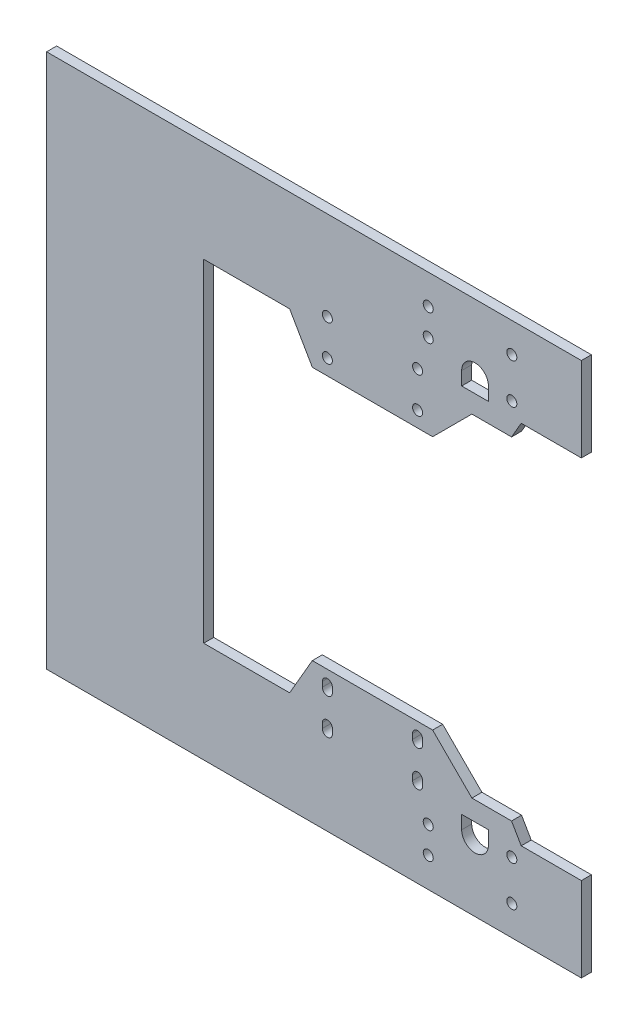
SolidWorks part; units mm, degrees
ref_plane "Front Plane" through (0, 0, 0) normal (0, 0, 1) x (1, 0, 0)
ref_plane "Top Plane" through (0, 0, 0) normal (0, 1, 0) x (1, 0, 0)
ref_plane "Right Plane" through (0, 0, 0) normal (1, 0, 0) x (0, 0, -1)
sketch "Sketch2" plane through (0, 0, 0) normal (0, 0, 1) x (1, 0, 0)
  line L0 (-102, 23.75) -> (-102, 0) construction
  line L1 (3, 49.75) -> (-110, 49.75)
  line L2 (3, 49.75) -> (3, -49.75)
  line L3 (3, -49.75) -> (-110, -49.75)
  line L4 (-110, 49.75) -> (-110, -49.75)
  line L5 (-97.0774, 39.75) -> (-88.9226, 39.75) construction
  line L6 (-77, 0) -> (-110, 0) construction
  line L7 (-77, -33) -> (-77, 33) construction
  line L10 (3, -30) -> (3, 30) construction
  line L11 (-110, 0) -> (-157, 0) construction
  line L12 (3, 80) -> (-157, 80)
  line L13 (3, 80) -> (3, -80)
  line L14 (3, -80) -> (-157, -80)
  line L15 (-157, 80) -> (-157, -80)
  dimension "D1" = 8
  dimension "D2" = 10
  dimension "D3" = 160
  dimension "D4" = 160
extrude "Boss-Extrude1" add sketch "Sketch2" along normal blind 3 contours L12 L15 L14 L13 L3 L4 L1
sketch "Sketch3" plane through (0, 0, 3) normal (0, 0, 1) x (1, 0, 0)
  line L0 (-77.5, 38) -> (-41.5, 38)
  line L1 (-41.5, 38) -> (-29.75, 49.75)
  line L2 (3, 49.75) -> (-110, 49.75) construction
  line L3 (-29.75, 49.75) -> (-84.2839, 49.75)
  line L4 (-84.2839, 49.75) -> (-77.5, 38)
  line L5 (-77.5, 38) -> (-77.5, 55) construction
  line L6 (-110, 0) -> (98.0736, 0) construction
  line L7 (-110, 49.75) -> (-110, -49.75) construction
  line L8 (-29.75, -49.75) -> (-84.2839, -49.75)
  line L9 (-41.5, -38) -> (-29.75, -49.75)
  line L10 (-77.5, -38) -> (-41.5, -38)
  line L11 (-84.2839, -49.75) -> (-77.5, -38)
  dimension "D1" = 45
  dimension "D2" = 30
extrude "Boss-Extrude2" add sketch "Sketch3" against normal up to surface (3 mm away) up to face at (-65.25, 0, 0)
sketch "Sketch4" plane through (0, 0, 3) normal (0, 0, 1) x (1, 0, 0)
  line L0 (-17.8868, -49.75) -> (-15, -54.75)
  line L1 (3, -49.75) -> (-29.75, -49.75) construction
  line L2 (-15, -54.75) -> (3, -54.75)
  line L3 (3, -49.75) -> (3, -80) construction
  line L4 (3, -54.75) -> (3, -49.75)
  line L5 (3, -49.75) -> (-17.8868, -49.75)
  line L6 (-110, 0) -> (99.4713, 0) construction
  line L7 (-110, 49.75) -> (-110, -49.75) construction
  line L8 (-17.8868, 49.75) -> (-15, 54.75)
  line L9 (3, 49.75) -> (-17.8868, 49.75)
  line L10 (3, 54.75) -> (3, 49.75)
  line L11 (-15, 54.75) -> (3, 54.75)
  dimension "D1" = 18
  dimension "D2" = 5
  dimension "D3" = 60
extrude "Cut-Extrude1" cut sketch "Sketch4" against normal through all
sketch "Sketch5" plane through (0, 0, 3) normal (0, 0, 1) x (1, 0, 0)
  circle A0 centre (-73, -42.65) radius 1.5 construction
  circle A1 centre (-46, -42.65) radius 1.5 construction
  circle A2 centre (-73, -42.65) radius 1.5
  circle A3 centre (-46, -42.65) radius 1.5
  circle A4 centre (-46, -53.35) radius 1.5 construction
  circle A5 centre (-73, -53.35) radius 1.5 construction
  circle A6 centre (-46, -53.35) radius 1.5
  circle A7 centre (-73, -53.35) radius 1.5
  circle A8 centre (-46, 42.65) radius 1.5 construction
  circle A9 centre (-73, 42.65) radius 1.5 construction
  circle A10 centre (-46, 42.65) radius 1.5
  circle A11 centre (-73, 42.65) radius 1.5
  circle A12 centre (-73, 53.35) radius 1.5 construction
  circle A13 centre (-73, 53.35) radius 1.5
  circle A14 centre (-46, 53.35) radius 1.5 construction
  circle A15 centre (-46, 53.35) radius 1.5
extrude "Cut-Extrude2" cut sketch "Sketch5" against normal blind 10
sketch "Sketch7" plane through (0, 0, 0) normal (0, 0, -1) x (-1, 0, 0)
  circle A0 centre (28.8114, -59.5) radius 4 construction
  circle A1 centre (28.8114, -59.5) radius 4
  circle A2 centre (28.8114, 59.5) radius 4 construction
  circle A3 centre (28.8114, 59.5) radius 4
extrude "Cut-Extrude3" cut sketch "Sketch7" against normal blind 6
sketch "Sketch8" plane through (0, 0, 3) normal (0, 0, 1) x (1, 0, 0)
  circle A0 centre (-17.8114, 59.1) radius 1.5 construction
  circle A1 centre (-17.8114, 71.1) radius 1.5 construction
  circle A2 centre (-42.8114, 63.1) radius 1.5 construction
  circle A3 centre (-42.8114, 71.1) radius 1.5 construction
  circle A4 centre (-42.8114, -71.1) radius 1.5 construction
  circle A5 centre (-42.8114, -63.1) radius 1.5 construction
  circle A6 centre (-17.8114, -59.1) radius 1.5 construction
  circle A7 centre (-17.8114, -71.1) radius 1.5 construction
  circle A8 centre (-17.8114, 59.1) radius 1.5
  circle A9 centre (-17.8114, 71.1) radius 1.5
  circle A10 centre (-42.8114, 63.1) radius 1.5
  circle A11 centre (-42.8114, 71.1) radius 1.5
  circle A12 centre (-42.8114, -71.1) radius 1.5
  circle A13 centre (-42.8114, -63.1) radius 1.5
  circle A14 centre (-17.8114, -59.1) radius 1.5
  circle A15 centre (-17.8114, -71.1) radius 1.5
extrude "Cut-Extrude4" cut sketch "Sketch8" against normal blind 4
sketch "Sketch9" plane through (0, 0, 0) normal (0, 0, -1) x (-1, 0, 0)
  line L0 (24.8114, 59.5) -> (24.8114, 55.5)
  line L1 (24.8114, 55.5) -> (32.8114, 55.5)
  line L2 (32.8114, 55.5) -> (32.8114, 59.5)
  line L3 (24.8114, -59.5) -> (24.8114, -55.5)
  line L4 (24.8114, -55.5) -> (28.8114, -55.5)
  line L5 (28.8114, -55.5) -> (32.8114, -55.5)
  line L6 (32.8114, -55.5) -> (32.8114, -59.5)
  line L7 (28.8114, -59.5) -> (28.8114, -55.5) construction
  circle A0 centre (28.8114, 59.5) radius 4 construction
  circle A1 centre (28.8114, 59.5) radius 4
  circle A2 centre (28.8114, -59.5) radius 4 construction
  circle A3 centre (28.8114, -59.5) radius 4
  circle M17 centre (28.8114, -59.5) radius 4
  circle M18 centre (28.8114, 59.5) radius 4
extrude "Cut-Extrude5" cut sketch "Sketch9" against normal blind 10 contours L6 L5 M17 | L4 L3 M17 | L0 L1 M18 | L1 L2 M18
sketch "Sketch10" plane through (0, 0, 0) normal (0, 0, -1) x (-1, 0, 0)
  line L0 (73, -54.1) -> (73, -52.6) construction
  line L1 (71.5, -54.1) -> (71.5, -52.6)
  line L2 (74.5, -54.1) -> (74.5, -52.6)
  line L3 (73, -41.9) -> (73, -43.4) construction
  line L4 (74.5, -41.9) -> (74.5, -43.4)
  line L5 (71.5, -41.9) -> (71.5, -43.4)
  line L6 (46, -54.1) -> (46, -52.6) construction
  line L7 (44.5, -54.1) -> (44.5, -52.6)
  line L8 (47.5, -54.1) -> (47.5, -52.6)
  line L9 (46, -41.9) -> (46, -43.4) construction
  line L10 (47.5, -41.9) -> (47.5, -43.4)
  line L11 (44.5, -41.9) -> (44.5, -43.4)
  circle A0 centre (46, -42.65) radius 1.5 construction
  circle A1 centre (46, -53.35) radius 1.5 construction
  circle A2 centre (73, -42.65) radius 1.5 construction
  circle A3 centre (73, -53.35) radius 1.5 construction
  circle A4 centre (46, -42.65) radius 1.5
  circle A5 centre (46, -53.35) radius 1.5
  circle A6 centre (73, -42.65) radius 1.5
  circle A7 centre (73, -53.35) radius 1.5
  arc A8 (71.5, -54.1) -> (74.5, -54.1) centre (73, -54.1) ccw
  arc A9 (74.5, -52.6) -> (71.5, -52.6) centre (73, -52.6) ccw
  arc A10 (74.5, -41.9) -> (71.5, -41.9) centre (73, -41.9) ccw
  arc A11 (71.5, -43.4) -> (74.5, -43.4) centre (73, -43.4) ccw
  arc A12 (44.5, -54.1) -> (47.5, -54.1) centre (46, -54.1) ccw
  arc A13 (47.5, -52.6) -> (44.5, -52.6) centre (46, -52.6) ccw
  arc A14 (47.5, -41.9) -> (44.5, -41.9) centre (46, -41.9) ccw
  arc A15 (44.5, -43.4) -> (47.5, -43.4) centre (46, -43.4) ccw
  point P14 (73, -53.35)
  point P21 (73, -42.65)
  point P27 (46, -53.35)
  point P34 (46, -42.65)
  circle M38 centre (73, -53.35) radius 1.5
  circle M39 centre (46, -53.35) radius 1.5
  circle M40 centre (46, -42.65) radius 1.5
  circle M44 centre (73, -42.65) radius 1.5
  dimension "D1" = 4.5
extrude "Cut-Extrude6" cut sketch "Sketch10" against normal through all contours L2 A9 L1 M38 | L1 A8 L2 M38 | L5 A11 L4 M44 | L4 A10 L5 M44 | L10 A14 L11 M40 | L11 A15 L10 M40 | L8 A13 L7 M39 | L7 A12 L8 M39
